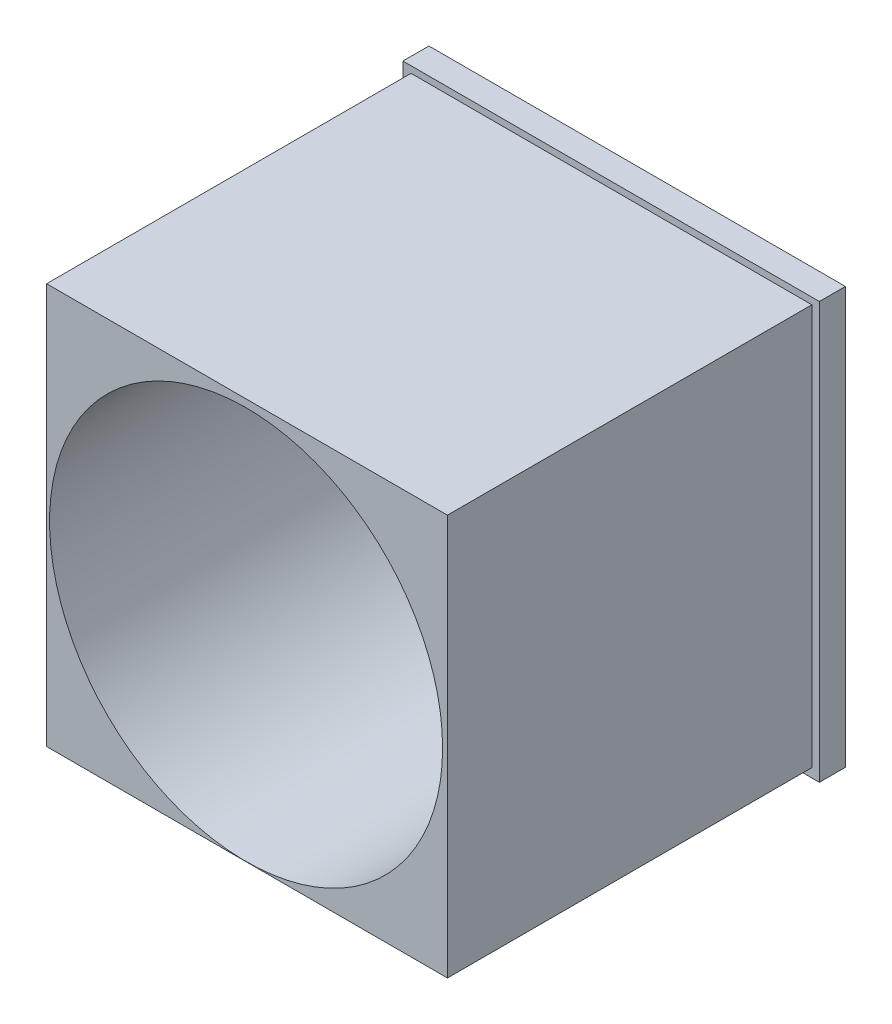
SolidWorks part; units mm, degrees
material "POLYURETHANE (11671)"
ref_plane "Front Plane" through (0, 0, 0) normal (0, 0, 1) x (1, 0, 0)
ref_plane "Top Plane" through (0, 0, 0) normal (0, 1, 0) x (1, 0, 0)
ref_plane "Right Plane" through (0, 0, 0) normal (1, 0, 0) x (0, 0, -1)
sketch "Sketch2" plane through (0, 0, 0) normal (0, 0, 1) x (1, 0, 0)
  line L1 (-19.883, 22.2865) -> (20.757, 22.2865)
  line L2 (-19.883, 22.2865) -> (-19.883, -18.3535)
  line L3 (-19.883, -18.3535) -> (20.757, -18.3535)
  line L4 (20.757, 22.2865) -> (20.757, -18.3535)
  dimension "D1" = 40.64
  dimension "D2" = 40.64
extrude "Boss-Extrude1" add sketch "Sketch2" along normal blind 38.1 contours L2 L1 L4 L3
sketch "Sketch3" plane through (0, 0, 38.1) normal (0, 0, 1) x (1, 0, 0)
  line L1 (-19.0911, 21.6424) -> (20.0249, 21.6424)
  line L2 (-19.0911, 21.6424) -> (-19.0911, -17.4736)
  line L3 (-19.0911, -17.4736) -> (20.0249, -17.4736)
  line L4 (20.0249, 21.6424) -> (20.0249, -17.4736)
  line M5 (-19.883, -18.3535) -> (20.757, -18.3535)
  line M6 (20.757, -18.3535) -> (20.757, 22.2865)
  line M7 (20.757, 22.2865) -> (-19.883, 22.2865)
  line M8 (-19.883, 22.2865) -> (-19.883, -18.3535)
  dimension "D1" = 39.116
  dimension "D2" = 39.116
extrude "Cut-Extrude1" cut sketch "Sketch3" against normal blind 35.56 contours L1 L4 L3 L2 M8 M5 M6 M7
sketch "Sketch4" plane through (0, 0, 38.1) normal (0, 0, 1) x (1, 0, 0)
  circle A1 centre (0.3753, 1.7197) radius 19.177
  dimension "D1" = 38.354
extrude "Cut-Extrude3" cut sketch "Sketch4" against normal blind 35.56
